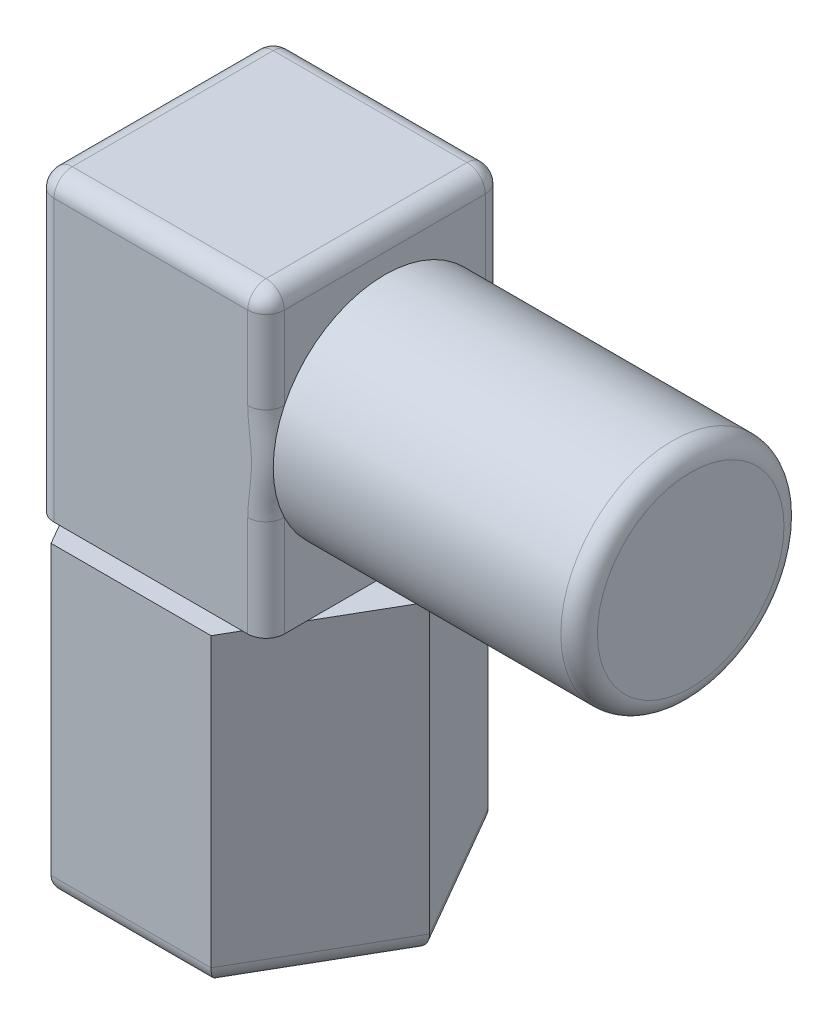
SolidWorks part; units mm, degrees
ref_plane "Front Plane" through (0, 0, 0) normal (0, 0, 1) x (1, 0, 0)
ref_plane "Top Plane" through (0, 0, 0) normal (0, 1, 0) x (1, 0, 0)
ref_plane "Right Plane" through (0, 0, 0) normal (1, 0, 0) x (0, 0, -1)
sketch "Sketch1" plane through (0, 0, 0) normal (0, 1, 0) x (1, 0, 0)
  line L1 (4.4456, 0) -> (2.2228, 3.85)
  line L2 (2.2228, 3.85) -> (-2.2228, 3.85)
  line L3 (-2.2228, 3.85) -> (-4.4456, 0)
  line L4 (-4.4456, 0) -> (-2.2228, -3.85)
  line L5 (-2.2228, -3.85) -> (2.2228, -3.85)
  line L6 (2.2228, -3.85) -> (4.4456, 0)
  circle A0 centre (0, 0) radius 4.4456 construction
  dimension "D1" = 7.7
extrude "Boss-Extrude1" add sketch "Sketch1" along normal blind 8.5
sketch "Sketch2" plane through (0, 8.5, 0) normal (0, 1, 0) x (1, 0, 0)
  line L0 (-3.2, 3.3) -> (3.2, -3.3) construction
  line L1 (-3.2, 3.3) -> (3.2, 3.3)
  line L2 (-3.2, 3.3) -> (-3.2, -3.3)
  line L3 (-3.2, -3.3) -> (3.2, -3.3)
  line L4 (3.2, 3.3) -> (3.2, -3.3)
  point P4 (0, 0)
  point P5 (0, 0)
  dimension "D1" = 6.4
  dimension "D2" = 6.6
extrude "Boss-Extrude2" add sketch "Sketch2" along normal blind 8.3
sketch "Sketch3" plane through (3.2, 0, 0) normal (1, 0, 0) x (0, 0, -1)
  line L0 (-3.3, 16.8) -> (3.3, 8.5) construction
  circle A0 centre (0, 12.65) radius 3.1
  dimension "D1" = 6.2
extrude "Boss-Extrude3" add sketch "Sketch3" along normal blind 8.5 contours A0
sketch "Sketch4" plane through (0, 0, 0) normal (0, -1, 0) x (1, 0, 0)
  circle A0 centre (0, 0) radius 3.1
  dimension "D1" = 6.2
extrude "Cut-Extrude1" cut sketch "Sketch4" against normal up to surface (8.5 mm away) contours A0 up to face at (2.9801, 8.5, 2.9191)
fillet "Fillet1" radius 0.508 15 edges at (11.7, 12.65, -3.1) (-3.3342, 0, 1.925) (-3.3342, 0, -1.925) (0, 0, -3.85) (3.3342, 0, -1.925) (3.3342, 0, 1.925) (0, 0, 3.85) (3.2, 12.65, 3.3) (3.2, 12.65, -3.3) (3.2, 16.8, 0) (0, 16.8, -3.3) (-3.2, 12.65, -3.3) (-3.2, 16.8, 0) (0, 16.8, 3.3) (-3.2, 12.65, 3.3)
